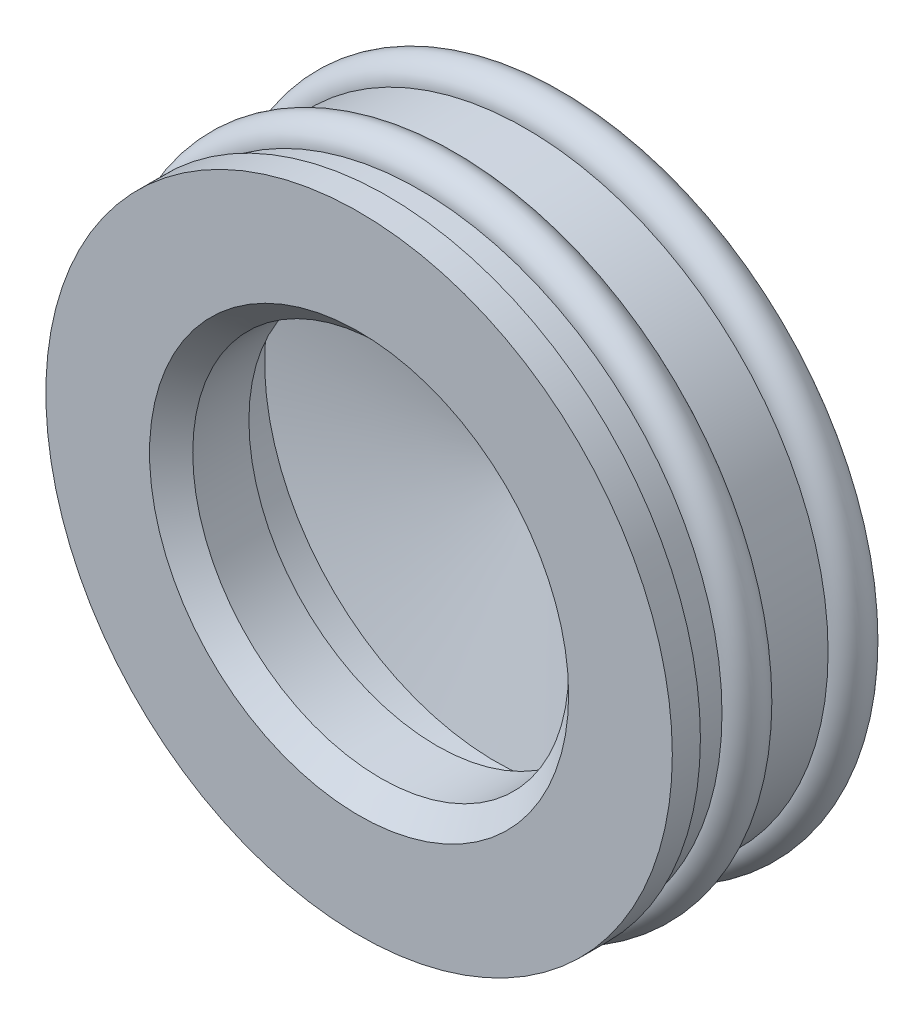
SolidWorks part; units mm, degrees
ref_plane "前视基准面" through (0, 0, 0) normal (0, 0, 1) x (1, 0, 0)
ref_plane "上视基准面" through (0, 0, 0) normal (0, 1, 0) x (1, 0, 0)
ref_plane "右视基准面" through (0, 0, 0) normal (1, 0, 0) x (0, 0, -1)
sketch "草图1" plane through (0, 0, 0) normal (0, 1, 0) x (1, 0, 0)
  line L0 (0, 12.8024) -> (0, 8.8024)
  line L1 (0.6982, 8.72) -> (10.7, 6.3266)
  line L2 (10.7, 6.3266) -> (10.7, 3.6)
  line L3 (10.7, 3.6) -> (8.7, 3.6)
  line L4 (8.7, 3.6) -> (8.7, 1)
  line L5 (8.7, 1) -> (9.7, 0)
  line L6 (9.7, 0) -> (14.5, 0)
  line L7 (14.5, 0) -> (14.5, 1.3)
  line L8 (14.5, 1.3) -> (14, 1.3)
  line L9 (14, 1.3) -> (14, 2.8)
  line L10 (14, 4.7115) -> (14, 7.7115)
  line L11 (14.2254, 9.596) -> (1.6291, 12.6102)
  line L12 (0, 12.8024) -> (0, 0) construction
  arc A0 (1.6291, 12.6102) -> (0, 12.8024) centre (0, 5.8024) ccw
  arc A1 (0, 8.8024) -> (0.6982, 8.72) centre (0, 5.8024) cw
  arc A2 (14, 2.8) -> (14, 4.7115) centre (14, 3.7557) ccw
  arc A3 (14, 7.7115) -> (14.2254, 9.596) centre (14, 8.6672) ccw
revolve "旋转1" add sketch "草图1" angle 360 about L12
